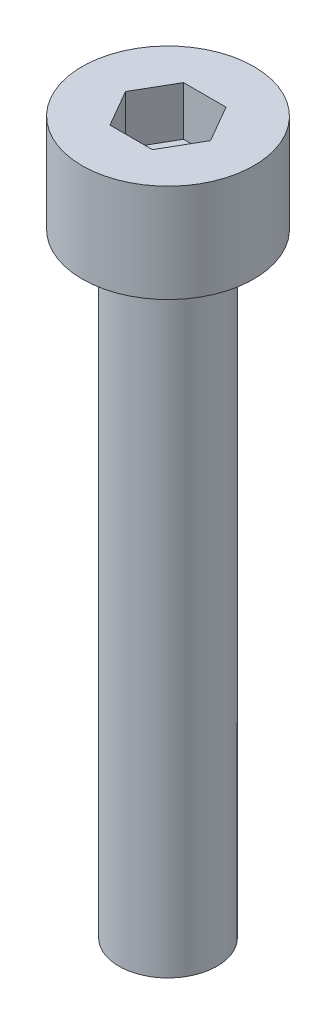
SolidWorks part; units mm, degrees
material "AISI 304"
ref_plane "前视基准面" through (0, 0, 0) normal (0, 0, 1) x (1, 0, 0)
ref_plane "上视基准面" through (0, 0, 0) normal (0, 1, 0) x (1, 0, 0)
ref_plane "右视基准面" through (0, 0, 0) normal (1, 0, 0) x (0, 0, -1)
sketch "草图1" plane through (0, 0, 0) normal (0, 1, 0) x (1, 0, 0)
  circle A0 centre (0, 0) radius 3.5
  dimension "D1" = 7
extrude "杯头" add sketch "草图1" along normal blind 4
sketch "草图2" plane through (0, 4, 0) normal (0, 1, 0) x (1, 0, 0)
  line L1 (1.7321, 0) -> (0.866, 1.5)
  line L2 (0.866, 1.5) -> (-0.866, 1.5)
  line L3 (-0.866, 1.5) -> (-1.7321, 0)
  line L4 (-1.7321, 0) -> (-0.866, -1.5)
  line L5 (-0.866, -1.5) -> (0.866, -1.5)
  line L6 (0.866, -1.5) -> (1.7321, 0)
  circle A0 centre (0, 0) radius 1.5 construction
  dimension "D1" = 3
extrude "内六角口" cut sketch "草图2" against normal blind 2
sketch "草图3" plane through (0, 0, 0) normal (0, -1, 0) x (1, 0, 0)
  circle A0 centre (0, 0) radius 2
  dimension "D1" = 4
extrude "螺纹长度" add sketch "草图3" along normal blind 25
